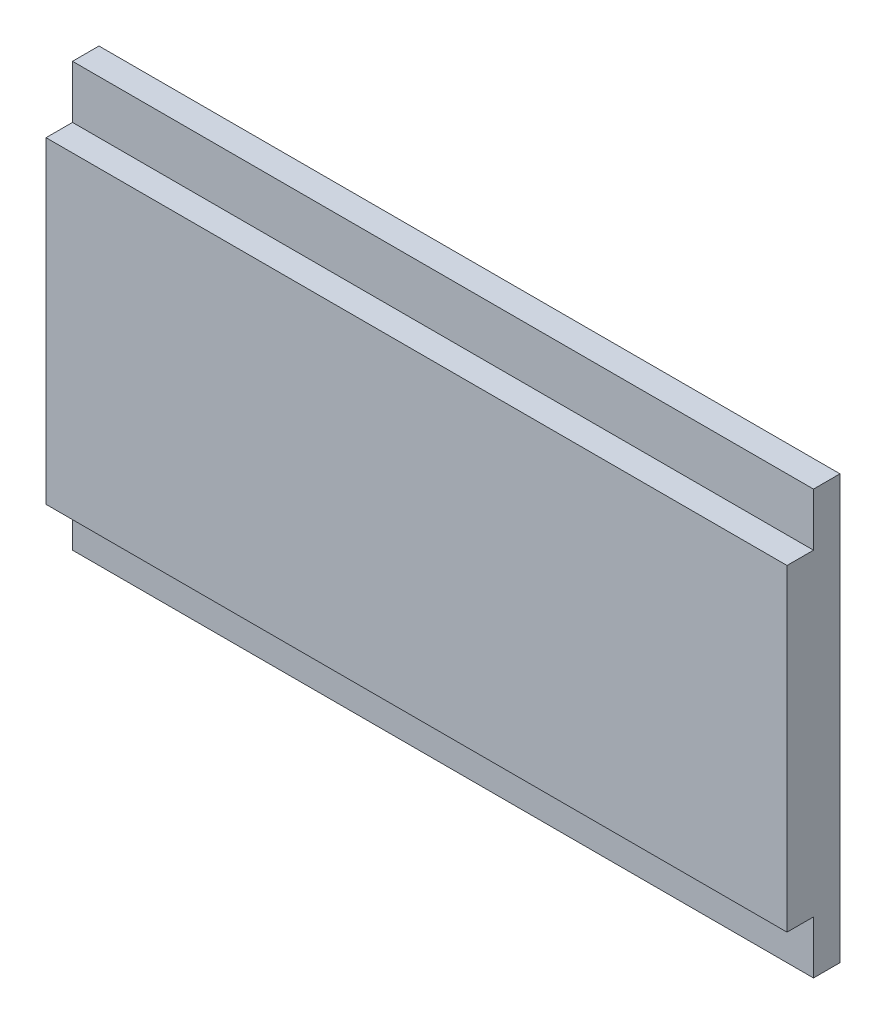
SolidWorks part; units mm, degrees
ref_plane "Front Plane" through (0, 0, 0) normal (0, 0, 1) x (1, 0, 0)
ref_plane "Top Plane" through (0, 0, 0) normal (0, 1, 0) x (1, 0, 0)
ref_plane "Right Plane" through (0, 0, 0) normal (1, 0, 0) x (0, 0, -1)
sketch "Sketch1" plane through (0, 0, 0) normal (0, 0, 1) x (1, 0, 0)
  line L2 (-44.45, -19.05) -> (44.45, -19.05)
  line L3 (-44.45, -19.05) -> (-44.45, 19.05)
  line L4 (-44.45, 19.05) -> (44.45, 19.05)
  line L5 (44.45, -19.05) -> (44.45, 19.05)
  line L6 (-44.45, -19.05) -> (44.45, 19.05) construction
  line L7 (-44.45, 19.05) -> (44.45, -19.05) construction
  point P1 (0, 0)
  dimension "D1" = 38.1
  dimension "D2" = 88.9
extrude "Boss-Extrude1" add sketch "Sketch1" along normal blind 6.35
sketch "Sketch2" plane through (0, 0, 0) normal (0, 0, -1) x (-1, 0, 0)
  line L1 (-44.45, 19.05) -> (44.45, 19.05)
  line L2 (-44.45, 19.05) -> (-44.45, 25.4)
  line L3 (-44.45, 25.4) -> (44.45, 25.4)
  line L4 (44.45, 19.05) -> (44.45, 25.4)
  line L5 (-44.45, -19.05) -> (44.45, -19.05)
  line L6 (-44.45, -19.05) -> (-44.45, -25.4)
  line L7 (-44.45, -25.4) -> (44.45, -25.4)
  line L8 (44.45, -19.05) -> (44.45, -25.4)
  dimension "D1" = 6.35
  dimension "D2" = 6.35
extrude "Boss-Extrude2" add sketch "Sketch2" against normal blind 3.175
